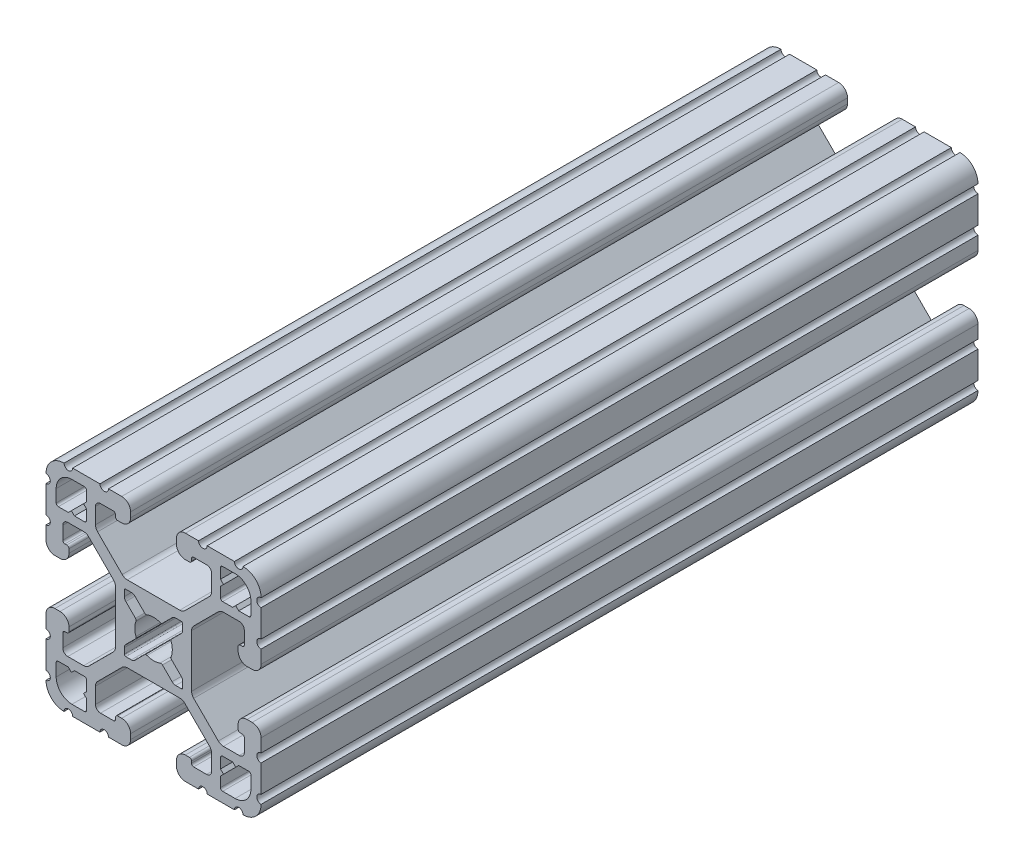
SolidWorks part; units mm, degrees
ref_plane "Front Plane" through (0, 0, 0) normal (0, 0, 1) x (1, 0, 0)
ref_plane "Top Plane" through (0, 0, 0) normal (0, 1, 0) x (1, 0, 0)
ref_plane "Right Plane" through (0, 0, 0) normal (1, 0, 0) x (0, 0, -1)
ref_plane "Plane1" through (0, 0, -2322.576) normal (0, 0, -1) x (-1, 0, 0)
sketch "Sketch1" plane through (0, 0, -2322.576) normal (0, 0, -1) x (-1, 0, 0)
  line L0 (17.2466, 14.4526) -> (17.2466, 12.2428)
  line L1 (16.8656, 11.8618) -> (15.0927, 11.8618)
  line L2 (15.0927, 11.8618) -> (14.5542, 12.4003)
  line L3 (14.5542, 12.4003) -> (14.0157, 11.8618)
  line L4 (14.0157, 11.8618) -> (12.2428, 11.8618)
  line L5 (11.8618, 12.2428) -> (11.8618, 14.0157)
  line L6 (11.8618, 14.0157) -> (12.4003, 14.5542)
  line L7 (12.4003, 14.5542) -> (11.8618, 15.0927)
  line L8 (11.8618, 15.0927) -> (11.8618, 16.8656)
  line L9 (12.2428, 17.2466) -> (14.4526, 17.2466)
  line L10 (17.2466, -12.2428) -> (17.2466, -14.4526)
  line L11 (14.4526, -17.2466) -> (12.2428, -17.2466)
  line L12 (11.8618, -16.8656) -> (11.8618, -15.0927)
  line L13 (11.8618, -15.0927) -> (12.4003, -14.5542)
  line L14 (12.4003, -14.5542) -> (11.8618, -14.0157)
  line L15 (11.8618, -14.0157) -> (11.8618, -12.2428)
  line L16 (12.2428, -11.8618) -> (14.0157, -11.8618)
  line L17 (14.0157, -11.8618) -> (14.5542, -12.4003)
  line L18 (14.5542, -12.4003) -> (15.0927, -11.8618)
  line L19 (15.0927, -11.8618) -> (16.8656, -11.8618)
  line L20 (5.1689, -3.9207) -> (5.1689, -4.9149)
  line L21 (4.9149, -5.1689) -> (3.9207, -5.1689)
  line L22 (3.2921, -4.9085) -> (1.5823, -3.1988)
  line L23 (-1.5823, -3.1988) -> (-3.2921, -4.9085)
  line L24 (-3.9207, -5.1689) -> (-4.9149, -5.1689)
  line L25 (-5.1689, -4.9149) -> (-5.1689, -3.9207)
  line L26 (-4.9085, -3.2921) -> (-3.1988, -1.5823)
  line L27 (-3.1988, 1.5823) -> (-4.9085, 3.2921)
  line L28 (-5.1689, 3.9207) -> (-5.1689, 4.9149)
  line L29 (-4.9149, 5.1689) -> (-3.9207, 5.1689)
  line L30 (-3.2921, 4.9085) -> (-1.5823, 3.1988)
  line L31 (1.5823, 3.1988) -> (3.2921, 4.9085)
  line L32 (3.9207, 5.1689) -> (4.9149, 5.1689)
  line L33 (5.1689, 4.9149) -> (5.1689, 3.9207)
  line L34 (4.9085, 3.2921) -> (3.1988, 1.5823)
  line L35 (3.1988, -1.5823) -> (4.9085, -3.2921)
  line L36 (-11.8618, -12.2428) -> (-11.8618, -14.0157)
  line L37 (-11.8618, -14.0157) -> (-12.4003, -14.5542)
  line L38 (-12.4003, -14.5542) -> (-11.8618, -15.0927)
  line L39 (-11.8618, -15.0927) -> (-11.8618, -16.8656)
  line L40 (-12.2428, -17.2466) -> (-14.4526, -17.2466)
  line L41 (-17.2466, -14.4526) -> (-17.2466, -12.2428)
  line L42 (-16.8656, -11.8618) -> (-15.0927, -11.8618)
  line L43 (-15.0927, -11.8618) -> (-14.5542, -12.4003)
  line L44 (-14.5542, -12.4003) -> (-14.0157, -11.8618)
  line L45 (-14.0157, -11.8618) -> (-12.2428, -11.8618)
  line L46 (-11.8618, 16.8656) -> (-11.8618, 15.0927)
  line L47 (-11.8618, 15.0927) -> (-12.4003, 14.5542)
  line L48 (-12.4003, 14.5542) -> (-11.8618, 14.0157)
  line L49 (-11.8618, 14.0157) -> (-11.8618, 12.2428)
  line L50 (-12.2428, 11.8618) -> (-14.0157, 11.8618)
  line L51 (-14.0157, 11.8618) -> (-14.5542, 12.4003)
  line L52 (-14.5542, 12.4003) -> (-15.0927, 11.8618)
  line L53 (-15.0927, 11.8618) -> (-16.8656, 11.8618)
  line L54 (-17.2466, 12.2428) -> (-17.2466, 14.4526)
  line L55 (-14.4526, 17.2466) -> (-12.2428, 17.2466)
  line L56 (19.05, -14.3256) -> (19.05, -9.4996)
  line L57 (19.05, -7.9756) -> (19.05, -5.6388)
  line L58 (17.4752, -4.064) -> (16.5608, -4.064)
  line L59 (14.986, -5.6388) -> (14.986, -6.35)
  line L60 (15.367, -6.731) -> (15.6972, -6.731)
  line L61 (16.0782, -7.112) -> (16.0782, -9.398)
  line L62 (15.1892, -10.287) -> (12.3756, -10.287)
  line L63 (11.4776, -9.915) -> (7.1157, -5.5531)
  line L64 (6.7437, -4.6551) -> (6.7437, 4.6551)
  line L65 (7.1157, 5.5531) -> (11.4776, 9.915)
  line L66 (12.3756, 10.287) -> (15.1892, 10.287)
  line L67 (16.0782, 9.398) -> (16.0782, 7.112)
  line L68 (15.6972, 6.731) -> (15.367, 6.731)
  line L69 (14.986, 6.35) -> (14.986, 5.6388)
  line L70 (16.5608, 4.064) -> (17.4752, 4.064)
  line L71 (19.05, 5.6388) -> (19.05, 7.9756)
  line L72 (19.05, 9.4996) -> (19.05, 14.3256)
  line L73 (14.3256, 19.05) -> (9.4996, 19.05)
  line L74 (7.9756, 19.05) -> (5.6388, 19.05)
  line L75 (4.064, 17.4752) -> (4.064, 16.5608)
  line L76 (5.6388, 14.986) -> (6.35, 14.986)
  line L77 (6.731, 15.367) -> (6.731, 15.6972)
  line L78 (7.112, 16.0782) -> (9.398, 16.0782)
  line L79 (10.287, 15.1892) -> (10.287, 12.3756)
  line L80 (9.915, 11.4776) -> (5.5531, 7.1157)
  line L81 (4.6551, 6.7437) -> (-4.6551, 6.7437)
  line L82 (-5.5531, 7.1157) -> (-9.915, 11.4776)
  line L83 (-10.287, 12.3756) -> (-10.287, 15.1892)
  line L84 (-9.398, 16.0782) -> (-7.112, 16.0782)
  line L85 (-6.731, 15.6972) -> (-6.731, 15.367)
  line L86 (-6.35, 14.986) -> (-5.6388, 14.986)
  line L87 (-4.064, 16.5608) -> (-4.064, 17.4752)
  line L88 (-5.6388, 19.05) -> (-7.9756, 19.05)
  line L89 (-9.4996, 19.05) -> (-14.3256, 19.05)
  line L90 (-19.05, 14.3256) -> (-19.05, 9.4996)
  line L91 (-19.05, 7.9756) -> (-19.05, 5.6388)
  line L92 (-17.4752, 4.064) -> (-16.5608, 4.064)
  line L93 (-14.986, 5.6388) -> (-14.986, 6.35)
  line L94 (-15.367, 6.731) -> (-15.6972, 6.731)
  line L95 (-16.0782, 7.112) -> (-16.0782, 9.398)
  line L96 (-15.1892, 10.287) -> (-12.3756, 10.287)
  line L97 (-11.4776, 9.915) -> (-7.1157, 5.5531)
  line L98 (-6.7437, 4.6551) -> (-6.7437, -4.6551)
  line L99 (-7.1157, -5.5531) -> (-11.4776, -9.915)
  line L100 (-12.3756, -10.287) -> (-15.1892, -10.287)
  line L101 (-16.0782, -9.398) -> (-16.0782, -7.112)
  line L102 (-15.6972, -6.731) -> (-15.367, -6.731)
  line L103 (-14.986, -6.35) -> (-14.986, -5.6388)
  line L104 (-16.5608, -4.064) -> (-17.4752, -4.064)
  line L105 (-19.05, -5.6388) -> (-19.05, -7.9756)
  line L106 (-19.05, -9.4996) -> (-19.05, -14.3256)
  line L107 (-14.3256, -19.05) -> (-9.4996, -19.05)
  line L108 (-7.9756, -19.05) -> (-5.6388, -19.05)
  line L109 (-4.064, -17.4752) -> (-4.064, -16.5608)
  line L110 (-5.6388, -14.986) -> (-6.35, -14.986)
  line L111 (-6.731, -15.367) -> (-6.731, -15.6972)
  line L112 (-7.112, -16.0782) -> (-9.398, -16.0782)
  line L113 (-10.287, -15.1892) -> (-10.287, -12.3756)
  line L114 (-9.915, -11.4776) -> (-5.5531, -7.1157)
  line L115 (-4.6551, -6.7437) -> (4.6551, -6.7437)
  line L116 (5.5531, -7.1157) -> (9.915, -11.4776)
  line L117 (10.287, -12.3756) -> (10.287, -15.1892)
  line L118 (9.398, -16.0782) -> (7.112, -16.0782)
  line L119 (6.731, -15.6972) -> (6.731, -15.367)
  line L120 (6.35, -14.986) -> (5.6388, -14.986)
  line L121 (4.064, -16.5608) -> (4.064, -17.4752)
  line L122 (5.6388, -19.05) -> (7.9756, -19.05)
  line L123 (9.4996, -19.05) -> (14.3256, -19.05)
  arc A0 (17.2466, 12.2428) -> (16.8656, 11.8618) centre (16.8656, 12.2428) cw
  arc A1 (12.2428, 11.8618) -> (11.8618, 12.2428) centre (12.2428, 12.2428) cw
  arc A2 (11.8618, 16.8656) -> (12.2428, 17.2466) centre (12.2428, 16.8656) cw
  arc A3 (14.4526, 17.2466) -> (17.2466, 14.4526) centre (14.4526, 14.4526) cw
  arc A4 (17.2466, -14.4526) -> (14.4526, -17.2466) centre (14.4526, -14.4526) cw
  arc A5 (12.2428, -17.2466) -> (11.8618, -16.8656) centre (12.2428, -16.8656) cw
  arc A6 (11.8618, -12.2428) -> (12.2428, -11.8618) centre (12.2428, -12.2428) cw
  arc A7 (16.8656, -11.8618) -> (17.2466, -12.2428) centre (16.8656, -12.2428) cw
  arc A8 (5.1689, -4.9149) -> (4.9149, -5.1689) centre (4.9149, -4.9149) cw
  arc A9 (3.9207, -5.1689) -> (3.2921, -4.9085) centre (3.9207, -4.2799) cw
  arc A10 (1.5823, -3.1988) -> (1.178, -3.1119) centre (1.3129, -3.4682) ccw
  arc A11 (1.178, -3.1119) -> (-1.178, -3.1119) centre (0, 0) cw
  arc A12 (-1.178, -3.1119) -> (-1.5823, -3.1988) centre (-1.3129, -3.4682) ccw
  arc A13 (-3.2921, -4.9085) -> (-3.9207, -5.1689) centre (-3.9207, -4.2799) cw
  arc A14 (-4.9149, -5.1689) -> (-5.1689, -4.9149) centre (-4.9149, -4.9149) cw
  arc A15 (-5.1689, -3.9207) -> (-4.9085, -3.2921) centre (-4.2799, -3.9207) cw
  arc A16 (-3.1988, -1.5823) -> (-3.1119, -1.178) centre (-3.4682, -1.3129) ccw
  arc A17 (-3.1119, -1.178) -> (-3.1119, 1.178) centre (0, 0) cw
  arc A18 (-3.1119, 1.178) -> (-3.1988, 1.5823) centre (-3.4682, 1.3129) ccw
  arc A19 (-4.9085, 3.2921) -> (-5.1689, 3.9207) centre (-4.2799, 3.9207) cw
  arc A20 (-5.1689, 4.9149) -> (-4.9149, 5.1689) centre (-4.9149, 4.9149) cw
  arc A21 (-3.9207, 5.1689) -> (-3.2921, 4.9085) centre (-3.9207, 4.2799) cw
  arc A22 (-1.5823, 3.1988) -> (-1.178, 3.1119) centre (-1.3129, 3.4682) ccw
  arc A23 (-1.178, 3.1119) -> (1.178, 3.1119) centre (0, 0) cw
  arc A24 (1.178, 3.1119) -> (1.5823, 3.1988) centre (1.3129, 3.4682) ccw
  arc A25 (3.2921, 4.9085) -> (3.9207, 5.1689) centre (3.9207, 4.2799) cw
  arc A26 (4.9149, 5.1689) -> (5.1689, 4.9149) centre (4.9149, 4.9149) cw
  arc A27 (5.1689, 3.9207) -> (4.9085, 3.2921) centre (4.2799, 3.9207) cw
  arc A28 (3.1988, 1.5823) -> (3.1119, 1.178) centre (3.4682, 1.3129) ccw
  arc A29 (3.1119, 1.178) -> (3.1119, -1.178) centre (0, 0) cw
  arc A30 (3.1119, -1.178) -> (3.1988, -1.5823) centre (3.4682, -1.3129) ccw
  arc A31 (4.9085, -3.2921) -> (5.1689, -3.9207) centre (4.2799, -3.9207) cw
  arc A32 (-11.8618, -16.8656) -> (-12.2428, -17.2466) centre (-12.2428, -16.8656) cw
  arc A33 (-14.4526, -17.2466) -> (-17.2466, -14.4526) centre (-14.4526, -14.4526) cw
  arc A34 (-17.2466, -12.2428) -> (-16.8656, -11.8618) centre (-16.8656, -12.2428) cw
  arc A35 (-12.2428, -11.8618) -> (-11.8618, -12.2428) centre (-12.2428, -12.2428) cw
  arc A36 (-12.2428, 17.2466) -> (-11.8618, 16.8656) centre (-12.2428, 16.8656) cw
  arc A37 (-11.8618, 12.2428) -> (-12.2428, 11.8618) centre (-12.2428, 12.2428) cw
  arc A38 (-16.8656, 11.8618) -> (-17.2466, 12.2428) centre (-16.8656, 12.2428) cw
  arc A39 (-17.2466, 14.4526) -> (-14.4526, 17.2466) centre (-14.4526, 14.4526) cw
  arc A40 (19.05, -9.4996) -> (19.05, -7.9756) centre (19.05, -8.7376) cw
  arc A41 (19.05, -5.6388) -> (17.4752, -4.064) centre (17.4752, -5.6388) ccw
  arc A42 (16.5608, -4.064) -> (14.986, -5.6388) centre (16.5608, -5.6388) ccw
  arc A43 (14.986, -6.35) -> (15.367, -6.731) centre (15.367, -6.35) ccw
  arc A44 (15.6972, -6.731) -> (16.0782, -7.112) centre (15.6972, -7.112) cw
  arc A45 (16.0782, -9.398) -> (15.1892, -10.287) centre (15.1892, -9.398) cw
  arc A46 (12.3756, -10.287) -> (11.4776, -9.915) centre (12.3756, -9.017) cw
  arc A47 (7.1157, -5.5531) -> (6.7437, -4.6551) centre (8.0137, -4.6551) cw
  arc A48 (6.7437, 4.6551) -> (7.1157, 5.5531) centre (8.0137, 4.6551) cw
  arc A49 (11.4776, 9.915) -> (12.3756, 10.287) centre (12.3756, 9.017) cw
  arc A50 (15.1892, 10.287) -> (16.0782, 9.398) centre (15.1892, 9.398) cw
  arc A51 (16.0782, 7.112) -> (15.6972, 6.731) centre (15.6972, 7.112) cw
  arc A52 (15.367, 6.731) -> (14.986, 6.35) centre (15.367, 6.35) ccw
  arc A53 (14.986, 5.6388) -> (16.5608, 4.064) centre (16.5608, 5.6388) ccw
  arc A54 (17.4752, 4.064) -> (19.05, 5.6388) centre (17.4752, 5.6388) ccw
  arc A55 (19.05, 7.9756) -> (19.05, 9.4996) centre (19.05, 8.7376) cw
  arc A56 (19.05, 14.3256) -> (19.0499, 15.8496) centre (19.05, 15.0876) cw
  arc A57 (19.0499, 15.8496) -> (15.8496, 19.0499) centre (15.875, 15.875) ccw
  arc A58 (15.8496, 19.0499) -> (14.3256, 19.05) centre (15.0876, 19.05) cw
  arc A59 (9.4996, 19.05) -> (7.9756, 19.05) centre (8.7376, 19.05) cw
  arc A60 (5.6388, 19.05) -> (4.064, 17.4752) centre (5.6388, 17.4752) ccw
  arc A61 (4.064, 16.5608) -> (5.6388, 14.986) centre (5.6388, 16.5608) ccw
  arc A62 (6.35, 14.986) -> (6.731, 15.367) centre (6.35, 15.367) ccw
  arc A63 (6.731, 15.6972) -> (7.112, 16.0782) centre (7.112, 15.6972) cw
  arc A64 (9.398, 16.0782) -> (10.287, 15.1892) centre (9.398, 15.1892) cw
  arc A65 (10.287, 12.3756) -> (9.915, 11.4776) centre (9.017, 12.3756) cw
  arc A66 (5.5531, 7.1157) -> (4.6551, 6.7437) centre (4.6551, 8.0137) cw
  arc A67 (-4.6551, 6.7437) -> (-5.5531, 7.1157) centre (-4.6551, 8.0137) cw
  arc A68 (-9.915, 11.4776) -> (-10.287, 12.3756) centre (-9.017, 12.3756) cw
  arc A69 (-10.287, 15.1892) -> (-9.398, 16.0782) centre (-9.398, 15.1892) cw
  arc A70 (-7.112, 16.0782) -> (-6.731, 15.6972) centre (-7.112, 15.6972) cw
  arc A71 (-6.731, 15.367) -> (-6.35, 14.986) centre (-6.35, 15.367) ccw
  arc A72 (-5.6388, 14.986) -> (-4.064, 16.5608) centre (-5.6388, 16.5608) ccw
  arc A73 (-4.064, 17.4752) -> (-5.6388, 19.05) centre (-5.6388, 17.4752) ccw
  arc A74 (-7.9756, 19.05) -> (-9.4996, 19.05) centre (-8.7376, 19.05) cw
  arc A75 (-14.3256, 19.05) -> (-15.8496, 19.0499) centre (-15.0876, 19.05) cw
  arc A76 (-15.8496, 19.0499) -> (-19.0499, 15.8496) centre (-15.875, 15.875) ccw
  arc A77 (-19.0499, 15.8496) -> (-19.05, 14.3256) centre (-19.05, 15.0876) cw
  arc A78 (-19.05, 9.4996) -> (-19.05, 7.9756) centre (-19.05, 8.7376) cw
  arc A79 (-19.05, 5.6388) -> (-17.4752, 4.064) centre (-17.4752, 5.6388) ccw
  arc A80 (-16.5608, 4.064) -> (-14.986, 5.6388) centre (-16.5608, 5.6388) ccw
  arc A81 (-14.986, 6.35) -> (-15.367, 6.731) centre (-15.367, 6.35) ccw
  arc A82 (-15.6972, 6.731) -> (-16.0782, 7.112) centre (-15.6972, 7.112) cw
  arc A83 (-16.0782, 9.398) -> (-15.1892, 10.287) centre (-15.1892, 9.398) cw
  arc A84 (-12.3756, 10.287) -> (-11.4776, 9.915) centre (-12.3756, 9.017) cw
  arc A85 (-7.1157, 5.5531) -> (-6.7437, 4.6551) centre (-8.0137, 4.6551) cw
  arc A86 (-6.7437, -4.6551) -> (-7.1157, -5.5531) centre (-8.0137, -4.6551) cw
  arc A87 (-11.4776, -9.915) -> (-12.3756, -10.287) centre (-12.3756, -9.017) cw
  arc A88 (-15.1892, -10.287) -> (-16.0782, -9.398) centre (-15.1892, -9.398) cw
  arc A89 (-16.0782, -7.112) -> (-15.6972, -6.731) centre (-15.6972, -7.112) cw
  arc A90 (-15.367, -6.731) -> (-14.986, -6.35) centre (-15.367, -6.35) ccw
  arc A91 (-14.986, -5.6388) -> (-16.5608, -4.064) centre (-16.5608, -5.6388) ccw
  arc A92 (-17.4752, -4.064) -> (-19.05, -5.6388) centre (-17.4752, -5.6388) ccw
  arc A93 (-19.05, -7.9756) -> (-19.05, -9.4996) centre (-19.05, -8.7376) cw
  arc A94 (-19.05, -14.3256) -> (-19.0499, -15.8496) centre (-19.05, -15.0876) cw
  arc A95 (-19.0499, -15.8496) -> (-15.8496, -19.0499) centre (-15.875, -15.875) ccw
  arc A96 (-15.8496, -19.0499) -> (-14.3256, -19.05) centre (-15.0876, -19.05) cw
  arc A97 (-9.4996, -19.05) -> (-7.9756, -19.05) centre (-8.7376, -19.05) cw
  arc A98 (-5.6388, -19.05) -> (-4.064, -17.4752) centre (-5.6388, -17.4752) ccw
  arc A99 (-4.064, -16.5608) -> (-5.6388, -14.986) centre (-5.6388, -16.5608) ccw
  arc A100 (-6.35, -14.986) -> (-6.731, -15.367) centre (-6.35, -15.367) ccw
  arc A101 (-6.731, -15.6972) -> (-7.112, -16.0782) centre (-7.112, -15.6972) cw
  arc A102 (-9.398, -16.0782) -> (-10.287, -15.1892) centre (-9.398, -15.1892) cw
  arc A103 (-10.287, -12.3756) -> (-9.915, -11.4776) centre (-9.017, -12.3756) cw
  arc A104 (-5.5531, -7.1157) -> (-4.6551, -6.7437) centre (-4.6551, -8.0137) cw
  arc A105 (4.6551, -6.7437) -> (5.5531, -7.1157) centre (4.6551, -8.0137) cw
  arc A106 (9.915, -11.4776) -> (10.287, -12.3756) centre (9.017, -12.3756) cw
  arc A107 (10.287, -15.1892) -> (9.398, -16.0782) centre (9.398, -15.1892) cw
  arc A108 (7.112, -16.0782) -> (6.731, -15.6972) centre (7.112, -15.6972) cw
  arc A109 (6.731, -15.367) -> (6.35, -14.986) centre (6.35, -15.367) ccw
  arc A110 (5.6388, -14.986) -> (4.064, -16.5608) centre (5.6388, -16.5608) ccw
  arc A111 (4.064, -17.4752) -> (5.6388, -19.05) centre (5.6388, -17.4752) ccw
  arc A112 (7.9756, -19.05) -> (9.4996, -19.05) centre (8.7376, -19.05) cw
  arc A113 (14.3256, -19.05) -> (15.8496, -19.0499) centre (15.0876, -19.05) cw
  arc A114 (15.8496, -19.0499) -> (19.0499, -15.8496) centre (15.875, -15.875) ccw
  arc A115 (19.0499, -15.8496) -> (19.05, -14.3256) centre (19.05, -15.0876) cw
extrude "Boss-Extrude1" add sketch "Sketch1" against normal blind 127
